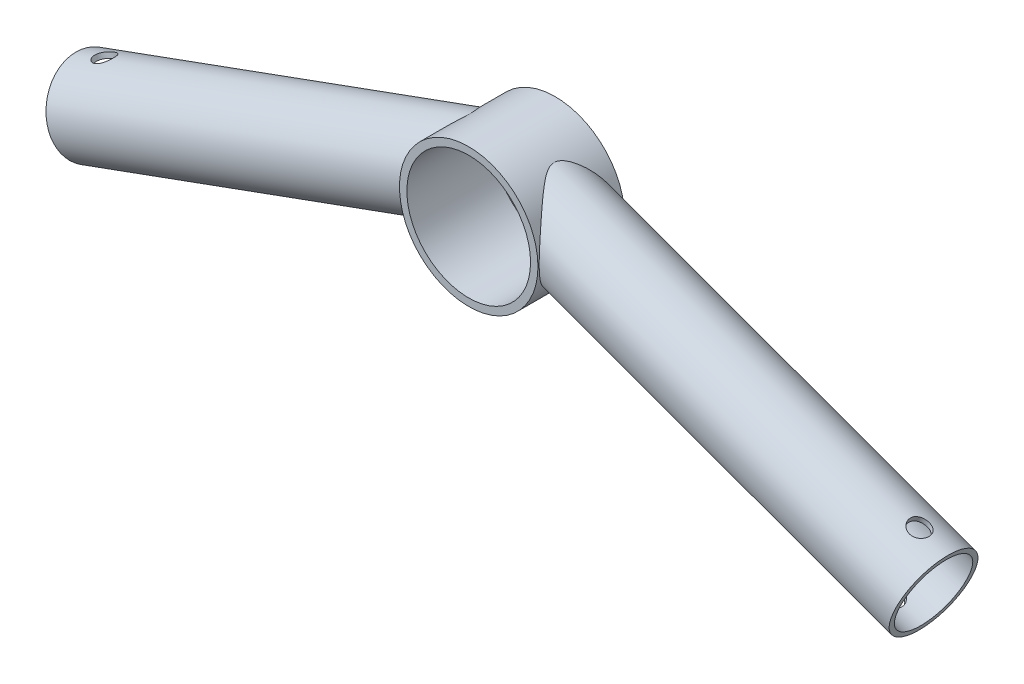
SolidWorks part; units mm, degrees
ref_plane "Plan de face" through (0, 0, 0) normal (0, 0, 1) x (1, 0, 0)
ref_plane "Plan de dessus" through (0, 0, 0) normal (0, 1, 0) x (1, 0, 0)
ref_plane "Plan de droite" through (0, 0, 0) normal (1, 0, 0) x (0, 0, -1)
sketch "Sketch1" plane through (0, 0, 0) normal (0, 0, 1) x (1, 0, 0)
  circle A0 centre (0, 0) radius 25
  circle A1 centre (0, 0) radius 28
  dimension "D1" = 50
  dimension "D2" = 56
extrude "Boss-Extrude1" add sketch "Sketch1" along normal blind 35
sketch "Sketch2" plane through (0, 0, 35) normal (0, 0, 1) x (1, 0, 0)
  line L0 (-0.9336, 0) -> (52.3589, 0) construction
  line L1 (28, 0) -> (62.4622, -12.5432) construction
  line L2 (0, 0) -> (0, 10.3014) construction
  line L3 (-28, 0) -> (-62.4622, -12.5432) construction
  line L4 (25.1677, -12.2714) -> (166.1216, -63.5744)
  line L5 (166.1216, -63.5744) -> (165.0955, -66.3935)
  line L6 (165.0955, -66.3935) -> (23.69, -14.926)
  line L7 (23.7348, 14.8546) -> (174.6721, -40.0821)
  line L8 (166.1216, -63.5744) -> (177.742, -31.6476) construction
  line L9 (174.6721, -40.0821) -> (175.764, -37.0821)
  line L10 (175.764, -37.0821) -> (19.9764, 19.62)
  line L11 (-166.1216, -63.5744) -> (-165.0955, -66.3935)
  line L12 (-165.0955, -66.3935) -> (-23.69, -14.926)
  line L13 (-25.1677, -12.2714) -> (-166.1216, -63.5744)
  line L14 (-23.7348, 14.8546) -> (-174.6721, -40.0821)
  line L15 (-174.6721, -40.0821) -> (-175.764, -37.0821)
  line L16 (-175.764, -37.0821) -> (-19.9764, 19.62)
  line L17 (19.9764, 19.62) -> (23.7348, 14.8546)
  line L18 (25.1677, -12.2714) -> (23.69, -14.926)
  line L19 (-25.1677, -12.2714) -> (-23.69, -14.926)
  line L20 (-19.9764, 19.62) -> (-23.7348, 14.8546)
  circle A0 centre (0, 0) radius 28 construction
  circle A2 centre (0, 0) radius 25 construction
  dimension "D7" = 0
  dimension "D1" = 20
  dimension "D2" = 12.5
  dimension "D3" = 3
  dimension "D4" = 150
  dimension "D5" = 12.5
  dimension "D6" = 3
  dimension "D8" = 0
ref_plane "Plane1" through (167.1215, -60.8272, 0) normal (0.9397, -0.342, 0) x (0, 0, -1)
sketch "Sketch3" plane through (167.1215, -60.8272, 0) normal (0.9397, -0.342, 0) x (0, 0, -1)
  line L0 (-32.5, 9.7078) -> (-2.5, 9.7078) construction
  circle A0 centre (-17.5, 9.7078) radius 15
  circle A1 centre (-17.5, 9.7078) radius 17
  dimension "D1" = 30
  dimension "D3" = 34
  dimension "D2" = 17.5
extrude "Boss-Extrude2" add sketch "Sketch3" against normal up to surface (164.6741 mm away)
mirror "Mirror1" about plane through (0, 0, 0) normal (1, 0, 0) of "Boss-Extrude2"
ref_plane "Plane2" through (9.1346, 25.0971, 0) normal (0.342, 0.9397, 0) x (0.9397, -0.342, 0)
sketch "Sketch4" plane through (9.1346, 25.0971, 0) normal (0.342, 0.9397, 0) x (0.9397, -0.342, 0)
  line L5 (0, -1.6928) -> (0, -41.7841) construction
  line L6 (28, 0) -> (-28, 0) construction
  line L7 (-187939.4014, -35) -> (187987.7255, -35) construction
  line L8 (0, -17.5) -> (36.1376, -17.5) construction
  circle A1 centre (165.7076, -17.5) radius 4
  point P6 (0, -17.5)
  dimension "D1" = 8
  dimension "D2" = 17.5
  dimension "D4" = 17.5
extrude "Cut-Extrude1" cut sketch "Sketch4" against normal through all
ref_plane "Plane3" through (0, 0, 34.5) normal (0, 0, 1) x (1, 0, 0)
mirror "Mirror2" about plane through (0, 0, 0) normal (1, 0, 0) of "Cut-Extrude1"
